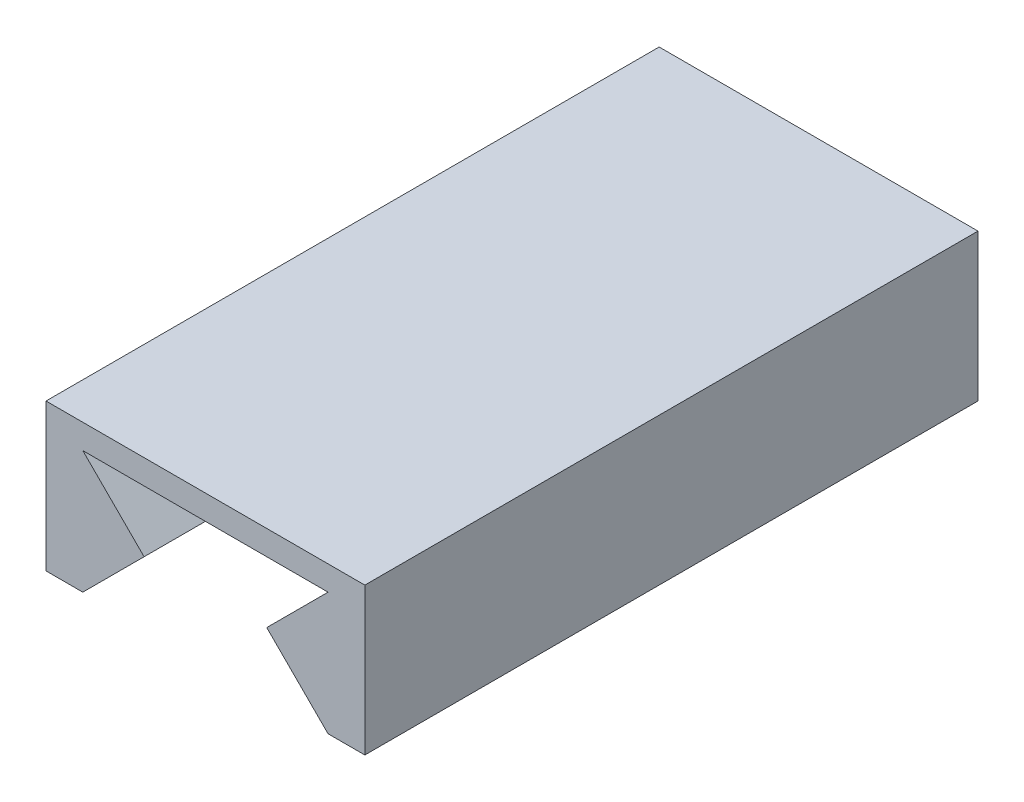
SolidWorks part; units mm, degrees
ref_plane "Ön Düzlem" through (0, 0, 0) normal (0, 0, 1) x (1, 0, 0)
ref_plane "Üst Düzlem" through (0, 0, 0) normal (0, 1, 0) x (1, 0, 0)
ref_plane "Sağ Düzlem" through (0, 0, 0) normal (1, 0, 0) x (0, 0, -1)
sketch "Çizim1" plane through (0, 0, 0) normal (0, 0, 1) x (1, 0, 0)
  line L0 (0, 0) -> (-5, -5)
  line L1 (0, 0) -> (-5, 5)
  line L2 (-5, 5) -> (15, 5)
  line L3 (15, 5) -> (10, 0)
  line L4 (10, 0) -> (15, -5)
  line L5 (15, -5) -> (18, -5)
  line L6 (18, -5) -> (18, 7)
  line L7 (18, 7) -> (-8, 7)
  line L8 (-8, 7) -> (-8, -5)
  line L9 (-8, -5) -> (-5, -5)
  dimension "D1" = 5
  dimension "D2" = 45
  dimension "D3" = 45
  dimension "D4" = 20
  dimension "D5" = 3
  dimension "D6" = 3
  dimension "D7" = 26
  dimension "D8" = 12
extrude "Yükseklik-Ekstrüzyon1" add sketch "Çizim1" along normal blind 50
